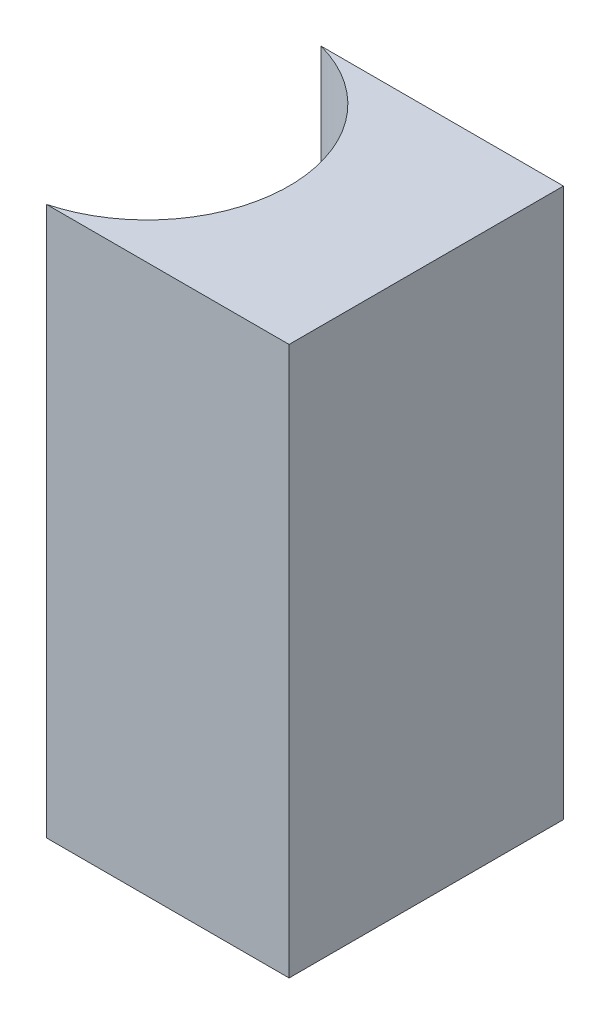
SolidWorks part; units mm, degrees
ref_plane "前视基准面" through (0, 0, 0) normal (0, 0, 1) x (1, 0, 0)
ref_plane "上视基准面" through (0, 0, 0) normal (0, 1, 0) x (1, 0, 0)
ref_plane "右视基准面" through (0, 0, 0) normal (1, 0, 0) x (0, 0, -1)
sketch "草图1" plane through (0, 0, 0) normal (0, 1, 0) x (1, 0, 0)
  line L0 (0, 0) -> (0, -4)
  line L1 (0, 0) -> (-3.5362, 0)
  line L2 (0, -4) -> (-3.5362, -4)
  line L3 (5.154, -2) -> (-4.9759, -2) construction
  arc A0 (-3.5362, -4) -> (-3.5362, 0) centre (-4.07, -2) ccw
  point P7 (-2, -2)
  point P8 (0, -2)
  dimension "D2" = 2.07
  dimension "D3" = 2
  dimension "D1" = 4
extrude "凸台-拉伸1" add sketch "草图1" along normal blind 8
